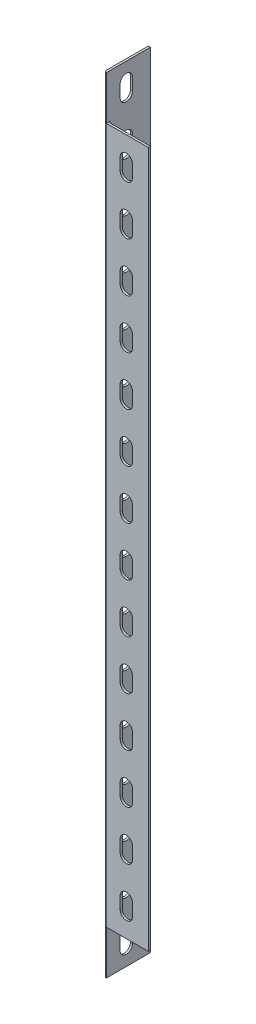
SolidWorks part; units mm, degrees
ref_plane "Front Plane" through (0, 0, 0) normal (0, 0, 1) x (1, 0, 0)
ref_plane "Top Plane" through (0, 0, 0) normal (0, 1, 0) x (1, 0, 0)
ref_plane "Right Plane" through (0, 0, 0) normal (1, 0, 0) x (0, 0, -1)
sketch "Sketch1" plane through (0, 0, 0) normal (0, 1, 0) x (1, 0, 0)
  line L0 (0, 0) -> (0, 25)
  line L1 (0, 0) -> (25, 0)
  dimension "D1" = 25
extrude "Extrude-Thin1" add sketch "Sketch1" along normal blind 450 thin
fillet "Fillet1" radius 1.2 2 edges at (1.2, 225, -1.2) (0, 225, 0)
sketch "Sketch2" plane through (0, 0, 0) normal (0, 0, 1) x (1, 0, 0)
  line L0 (12.5, 9.5) -> (12.5, 16.5) construction
  line L1 (9, 9.5) -> (9, 16.5)
  line L2 (16, 9.5) -> (16, 16.5)
  line L3 (1.2, 0) -> (25, 0) construction
  line L4 (25, 450) -> (25, 0) construction
  arc A0 (9, 9.5) -> (16, 9.5) centre (12.5, 9.5) ccw
  arc A1 (16, 16.5) -> (9, 16.5) centre (12.5, 16.5) ccw
  point P2 (12.5, 13)
  dimension "D1" = 3.5
  dimension "D3" = 9.5
  dimension "D2" = 7
  dimension "D4" = 12.5
extrude "Cut-Extrude1" cut sketch "Sketch2" against normal through all
pattern_linear "LPattern1" count 17 spacing 28 along (0, 1, 0) of "Cut-Extrude1"
pattern_circular "CirPattern1" count 2 every 270 about axis through (1.2, 450, 0) along (0, -1, 0) of "LPattern1", "Cut-Extrude1"
sketch "Sketch3" plane through (0, 450, 0) normal (0, 1, 0) x (1, 0, 0)
  line L6 (0, 25) -> (0, 1.2)
  line L7 (1.2, 0) -> (25, 0)
  line L8 (25, 0) -> (25, 1.2)
  line L9 (25, 1.2) -> (2.4, 1.2)
  line L10 (1.2, 2.4) -> (1.2, 25)
  line L11 (1.2, 25) -> (0, 25)
  line L12 (0, 25) -> (0, 1.2)
  line L13 (1.2, 0) -> (25, 0)
  line L14 (25, 0) -> (25, 1.2)
  line L15 (25, 1.2) -> (2.4, 1.2)
  line L16 (1.2, 2.4) -> (1.2, 25)
  line L17 (1.2, 25) -> (0, 25)
  arc A2 (0, 1.2) -> (1.2, 0) centre (1.2, 1.2) ccw
  arc A3 (1.2, 2.4) -> (2.4, 1.2) centre (2.4, 2.4) ccw
  arc A4 (0, 1.2) -> (1.2, 0) centre (1.2, 1.2) ccw
  arc A5 (1.2, 2.4) -> (2.4, 1.2) centre (2.4, 2.4) ccw
  dimension "D1" = 0
extrude "Cut-Extrude2" cut sketch "Sketch3" against normal blind 4
sketch "Sketch5" plane through (0, 0, 0) normal (0, 0, 1) x (1, 0, 0)
  line L1 (25, 446) -> (1.2, 446)
  line L2 (25, 446) -> (25, 421)
  line L3 (25, 421) -> (1.2, 421)
  line L4 (1.2, 446) -> (1.2, 421)
  line L5 (25, 0) -> (1.2, 0)
  line L6 (25, 0) -> (25, 25)
  line L7 (25, 25) -> (1.2, 25)
  line L8 (1.2, 0) -> (1.2, 25)
  dimension "D1" = 23.8
  dimension "D2" = 25
  dimension "D3" = 23.8
  dimension "D4" = 25
extrude "Cut-Extrude3" cut sketch "Sketch5" against normal blind 10
